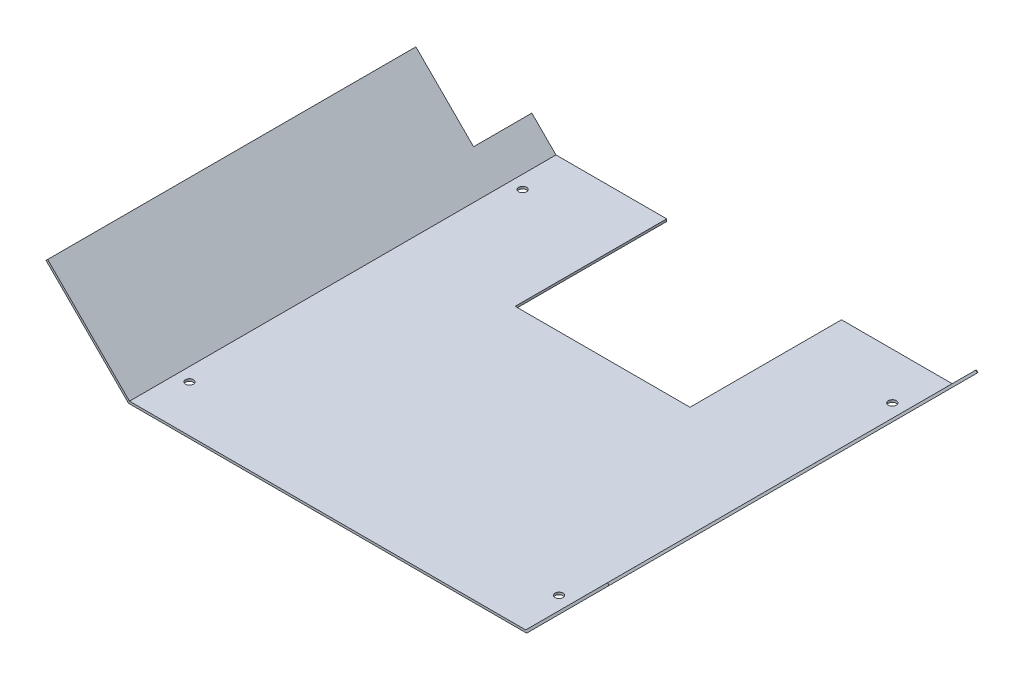
SolidWorks part; units mm, degrees
ref_plane "Plan de face" through (0, 0, 0) normal (0, 0, 1) x (1, 0, 0)
ref_plane "Plan de dessus" through (0, 0, 0) normal (0, 1, 0) x (1, 0, 0)
ref_plane "Plan de droite" through (0, 0, 0) normal (1, 0, 0) x (0, 0, -1)
sketch "Esquisse2" plane through (0, 0, 0) normal (0, 0, 1) x (1, 0, 0)
  line L0 (-59.1707, 35.114) -> (-24.0577, 0)
  line L1 (-24.0577, 0) -> (145.9423, 0)
  line L2 (145.9423, 0) -> (181.0563, 35.113)
  dimension "D1" = 170
  dimension "D2" = 49.658
  dimension "D3" = 49.658
  dimension "D4" = 35.114
extrude "Extru.-Mince1" add sketch "Esquisse2" along normal blind 183 thin
sketch "Esquisse8" plane through (0, 0, 0) normal (0, 1, 0) x (1, 0, 0)
  line L0 (-24.0577, 0) -> (145.9423, 0) construction
  line L1 (98.4423, 0) -> (23.4423, 0)
  line L2 (98.4423, 0) -> (98.4423, -65)
  line L3 (98.4423, -65) -> (23.4423, -65)
  line L4 (23.4423, 0) -> (23.4423, -65)
  line L5 (145.9423, -183) -> (145.9423, 0) construction
  line L6 (-24.0577, -183) -> (-24.0577, 0) construction
  dimension "D1" = 47.5
  dimension "D2" = 47.5
  dimension "D3" = 65
extrude "Enlèv. mat.-Extru.2" cut sketch "Esquisse8" against normal blind 1
sketch "Esquisse12" plane through (0, 0, 0) normal (0, 1, 0) x (1, 0, 0)
  line L0 (-24.0577, -183) -> (-24.0577, 0) construction
  line L1 (145.9423, -183) -> (145.9423, 0) construction
  line L2 (-24.0577, 0) -> (23.4423, 0) construction
  line L3 (-24.0577, -183) -> (145.9423, -183) construction
  line L4 (98.4423, 0) -> (145.9423, 0) construction
  point P0 (-18.3577, -20)
  point P1 (-18.3577, -163)
  point P2 (140.2423, -163)
  point P3 (140.2423, -20)
  dimension "D1" = 5.7
  dimension "D2" = 5.7
  dimension "D3" = 5.7
  dimension "D4" = 5.7
  dimension "D5" = 20
  dimension "D6" = 20
  dimension "D7" = 20
  dimension "D8" = 20
hole_wizard "Dégagement M32" positions "Esquisse14" profile "Esquisse13" hole size "M3" standard "ISO" end condition through all
sketch "Esquisse14" plane through (0, 0, 0) normal (0, 1, 0) x (-1, 0, 0)
  point P1 (18.3577, 20)
  point P4 (-140.2423, 20)
  point P7 (-140.2423, 163)
  point P10 (18.3577, 163)
sketch "Esquisse13" plane through (-18.3577, 0, 20) normal (1, 0, 0) x (0, 0, 1)
  line L0 (0, 0) -> (0, 1)
  line L1 (0, 1) -> (1.7, 1)
  line L2 (1.7, 1) -> (1.7, 0)
  line L5 (1.7, 0) -> (0, 0)
  line L11 (0, -6.35) -> (0, 107.95) construction
  dimension "Diamètre du perçage jusqu'au prochain" = 3.4
  dimension "Profondeur du perçage jusqu'au prochain" = 1
sketch "Esquisse15" plane through (-12.7363, -12.7359, 0) normal (-0.7071, -0.7071, 0) x (0, 0, 1)
  line L0 (183, 66.6691) -> (0, 66.6691) construction
  line L1 (0, 31.6691) -> (25, 31.6691)
  line L2 (0, 31.6691) -> (0, 66.6691)
  line L3 (0, 66.6691) -> (25, 66.6691)
  line L4 (25, 31.6691) -> (25, 66.6691)
  line L5 (0, 66.6691) -> (0, 16.5969) construction
  dimension "D1" = 25
  dimension "D2" = 35
  dimension "D3" = 0
extrude "Enlèv. mat.-Extru.3" cut sketch "Esquisse15" against normal up to next
sketch "Esquisse16" plane through (73.6762, -73.6783, 0) normal (0.7071, -0.7071, 0) x (0.7071, 0.7071, 0)
  line L0 (152.8562, 183) -> (152.8562, 0) construction
  line L1 (117.8562, 25) -> (152.8562, 25)
  line L2 (117.8562, 25) -> (117.8562, 0)
  line L3 (117.8562, 0) -> (152.8562, 0)
  line L4 (152.8562, 25) -> (152.8562, 0)
  line L5 (102.784, 0) -> (152.8562, 0) construction
  dimension "D1" = 25
  dimension "D2" = 0
  dimension "D3" = 35
extrude "Enlèv. mat.-Extru.4" cut sketch "Esquisse16" against normal up to next
